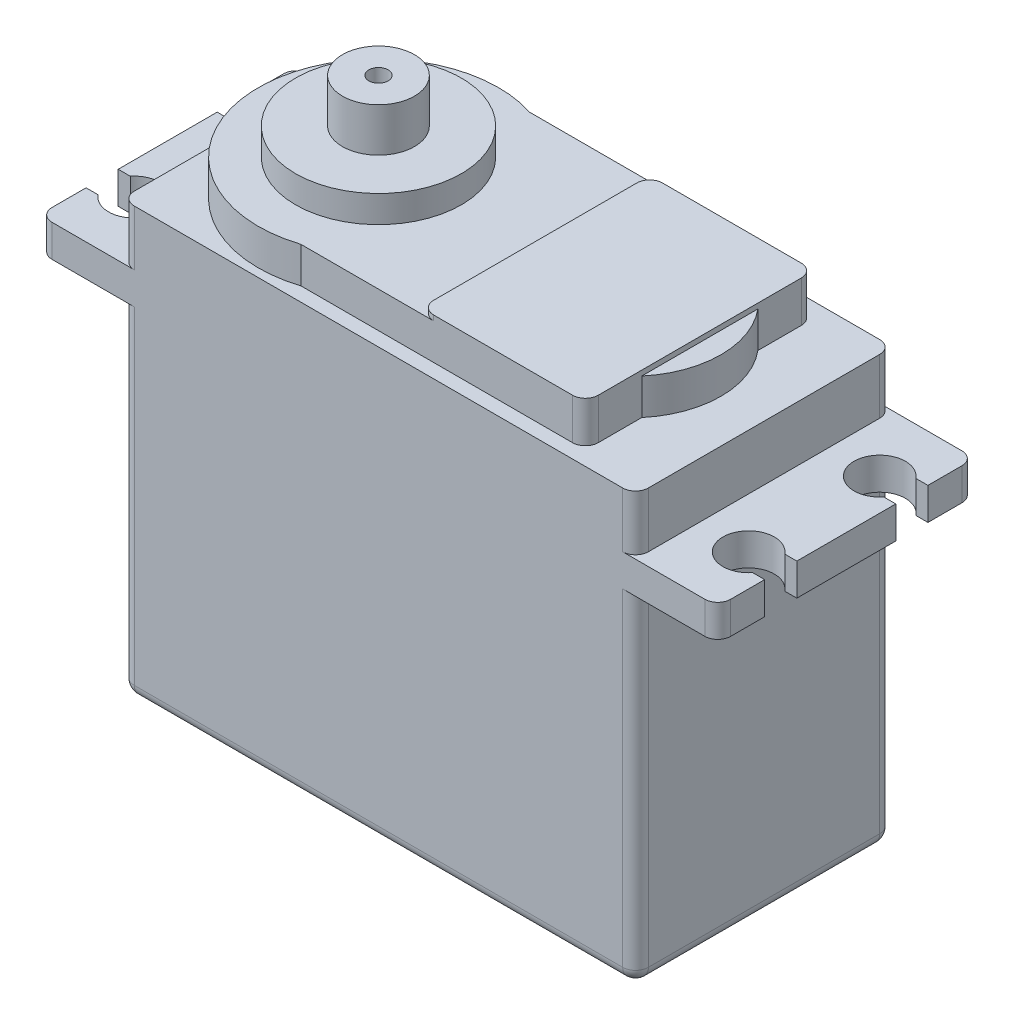
SolidWorks part; units mm, degrees
material "ABS PC"
ref_plane "Спереди" through (0, 0, 0) normal (0, 0, 1) x (1, 0, 0)
ref_plane "Сверху" through (0, 0, 0) normal (0, 1, 0) x (1, 0, 0)
ref_plane "Справа" through (0, 0, 0) normal (1, 0, 0) x (0, 0, -1)
sketch "Эскиз1" plane through (0, 0, 0) normal (0, 1, 0) x (1, 0, 0)
  line L1 (1, 0) -> (39, 0)
  line L2 (0, 1) -> (0, 19)
  line L3 (1, 20) -> (39, 20)
  line L4 (40, 1) -> (40, 19)
  arc A0 (1, 20) -> (0, 19) centre (1, 19) ccw
  arc A1 (40, 19) -> (39, 20) centre (39, 19) ccw
  arc A2 (39, 0) -> (40, 1) centre (39, 1) ccw
  arc A3 (0, 1) -> (1, 0) centre (1, 1) ccw
  point P13 (0, 0)
  dimension "D3" = 1
  dimension "D1" = 40
  dimension "D2" = 20
extrude "Вытянуть1" add sketch "Эскиз1" along normal blind 33.3
sketch "Эскиз2" plane through (0, 0, 0) normal (0, -1, 0) x (1, 0, 0)
  line L1 (-5.4, 0) -> (45.4, 0)
  line L2 (-6.4, -1) -> (-6.4, -19)
  line L3 (-5.4, -20) -> (45.4, -20)
  line L4 (46.4, -1) -> (46.4, -19)
  line L5 (39, -20) -> (1, -20) construction
  line L6 (1, 0) -> (39, 0) construction
  arc A0 (-5.4, 0) -> (-6.4, -1) centre (-5.4, -1) ccw
  arc A1 (46.4, -1) -> (45.4, 0) centre (45.4, -1) ccw
  arc A2 (-5.4, -20) -> (-6.4, -19) centre (-5.4, -19) cw
  arc A3 (46.4, -19) -> (45.4, -20) centre (45.4, -19) cw
  point P4 (20, 0)
  point P5 (20, 0)
  dimension "D2" = 1
  dimension "D1" = 52.8
extrude "Вытянуть2" add sketch "Эскиз2" against normal blind 2.5 from offset 26.5
sketch "Эскиз3" plane through (0, 33.3, 0) normal (0, 1, 0) x (1, 0, 0)
  line L0 (12.8657, 18.9) -> (34, 18.9)
  line L1 (35, 17.9) -> (35, 14.5141)
  line L2 (12.8657, 1.1) -> (34, 1.1)
  line L3 (35, 2.1) -> (35, 5.4859)
  line L5 (0.65, 10) -> (0.65, 20) construction
  line L6 (-5.4, 20) -> (1, 20) construction
  line L7 (0, 19) -> (0, 1) construction
  line L8 (36.65, 10) -> (36.65, 20) construction
  line L9 (40, 10) -> (0, 10) construction
  line L10 (40, 1) -> (40, 19) construction
  line L11 (39, 20) -> (1, 20) construction
  arc A0 (35, 17.9) -> (34, 18.9) centre (34, 17.9) ccw
  arc A1 (35, 14.5141) -> (35, 5.4859) centre (29.65, 10) cw
  arc A2 (12.8657, 18.9) -> (12.8657, 1.1) centre (10, 10) ccw
  arc A3 (34, 1.1) -> (35, 2.1) centre (34, 2.1) ccw
  dimension "D1" = 9.35
  dimension "D3" = 10
  dimension "D4" = 7
  dimension "D7" = 1
  dimension "D2" = 17.8
  dimension "D5" = 36
  dimension "D6" = 5
extrude "Вытянуть3" add sketch "Эскиз3" along normal blind 36.1 from surface at -33.3 contours L0 A2 L2 L3 A1 L1 starting at face at (20, 0, -10)
sketch "Эскиз5" plane through (0, 36.1, 0) normal (0, 1, 0) x (1, 0, 0)
  line L1 (23.2, 18.9) -> (34, 18.9)
  line L2 (22.2, 17.9) -> (22.2, 2.1)
  line L3 (23.2, 1.1) -> (34, 1.1)
  line L4 (35, 17.9) -> (35, 2.1)
  line L5 (12.8657, 1.1) -> (34, 1.1) construction
  line L6 (35, 5.4859) -> (35, 2.1) construction
  line L7 (34, 18.9) -> (12.8657, 18.9) construction
  line L9 (35, 17.9) -> (35, 14.5141) construction
  arc A0 (22.2, 17.9) -> (23.2, 18.9) centre (23.2, 17.9) cw
  arc A1 (23.2, 1.1) -> (22.2, 2.1) centre (23.2, 2.1) cw
  arc A2 (35, 2.1) -> (34, 1.1) centre (34, 2.1) cw
  arc A3 (34, 18.9) -> (35, 17.9) centre (34, 17.9) cw
  point P18 (35, 1.1)
  point P21 (35, 18.9)
  dimension "D2" = 1
  dimension "D1" = 12.8
extrude "Вытянуть4" add sketch "Эскиз5" along normal blind 0.4
sketch "Эскиз6" plane through (0, 36.1, 0) normal (0, 1, 0) x (1, 0, 0)
  circle A0 centre (10, 10) radius 6.45
  arc A1 (12.8657, 18.9) -> (12.8657, 1.1) centre (10, 10) ccw construction
  dimension "D1" = 12.9
extrude "Вытянуть5" add sketch "Эскиз6" along normal blind 2.1
sketch "Эскиз7" plane through (0, 38.2, 0) normal (0, 1, 0) x (1, 0, 0)
  circle A0 centre (10, 10) radius 2.8
  circle A1 centre (10, 10) radius 0.75
  dimension "D1" = 5.6
  dimension "D2" = 1.5
extrude "Вытянуть6" add sketch "Эскиз7" along normal blind 3.4 contours A0 A1
fillet "Скругление1" radius 1 8 edges at (39.7071, 0, -19.7071) (40, 0, -10) (39.7071, 0, -0.2929) (20, 0, 0) (0.2929, 0, -0.2929) (0, 0, -10) (0.2929, 0, -19.7071) (20, 0, -20)
sketch "Эскиз8" plane through (0, 29, 0) normal (0, 1, 0) x (1, 0, 0)
  line L0 (-3.9, 15.1) -> (43.9, 4.9) construction
  line L1 (43.9, 15.1) -> (-3.9, 4.9) construction
  line L2 (20, 20) -> (20, 0) construction
  line L3 (39, 20) -> (1, 20) construction
  line L4 (1, 0) -> (39, 0) construction
  line L5 (46.4, 10) -> (-6.4, 10) construction
  line L6 (46.4, 19) -> (46.4, 1) construction
  line L7 (-6.4, 1) -> (-6.4, 19) construction
  line L8 (45.4612, 16.35) -> (46.4, 16.35)
  line L9 (45.4612, 13.85) -> (46.4, 13.85)
  line L10 (45.4612, 6.15) -> (46.4, 6.15)
  line L11 (45.4612, 3.65) -> (46.4, 3.65)
  line L12 (-5.4612, 16.35) -> (-6.4, 16.35)
  line L13 (-5.4612, 13.85) -> (-6.4, 13.85)
  line L14 (-5.4612, 6.15) -> (-6.4, 6.15)
  line L15 (-5.4612, 3.65) -> (-6.4, 3.65)
  line L16 (45.4612, 16.35) -> (45.4612, 13.85)
  line L17 (46.4, 13.85) -> (46.4, 16.35)
  line L18 (45.4612, 6.15) -> (45.4612, 3.65)
  line L19 (46.4, 6.15) -> (46.4, 3.65)
  line L20 (-5.4612, 16.35) -> (-5.4612, 13.85)
  line L21 (-6.4, 16.35) -> (-6.4, 13.85)
  line L22 (-5.4612, 6.15) -> (-5.4612, 3.65)
  line L23 (-6.4, 6.15) -> (-6.4, 3.65)
  circle A0 centre (-3.9, 15.1) radius 2
  circle A1 centre (-3.9, 4.9) radius 2
  circle A2 centre (43.9, 4.9) radius 2
  circle A3 centre (43.9, 15.1) radius 2
  point P20 (20, 10)
  point P21 (20, 10)
  line M5 (-6.4, 19) -> (-6.4, 1)
  dimension "D1" = 47.8
  dimension "D2" = 10.2
  dimension "D3" = 4
  dimension "D4" = 2.5
extrude "Вырез-Вытянуть1" cut sketch "Эскиз8" against normal up to next contours A1 | A0 | A3 | A2 | A0 L12 L13 M5 | L20 A0 | L22 A1 | A1 L14 L15 M5 | L16 A3 | A3 L9 L17 L8 | L18 A2 | A2 L11 L19 L10
sketch "Эскиз10" plane through (0, 0, 0) normal (-1, 0, 0) x (0, 0, 1)
  line L1 (-12, 0.5) -> (-8, 0.5)
  line L2 (-13, 1.5) -> (-13, 3.5)
  line L3 (-12, 4.5) -> (-8, 4.5)
  line L4 (-7, 1.5) -> (-7, 3.5)
  line L5 (-19, 1) -> (-1, 1) construction
  line L6 (-1, 0) -> (-19, 0) construction
  arc A0 (-13, 3.5) -> (-12, 4.5) centre (-12, 3.5) cw
  arc A1 (-12, 0.5) -> (-13, 1.5) centre (-12, 1.5) cw
  arc A2 (-7, 1.5) -> (-8, 0.5) centre (-8, 1.5) cw
  arc A3 (-8, 4.5) -> (-7, 3.5) centre (-8, 3.5) cw
  point P4 (-10, 0.5)
  point P5 (-10, 1)
  dimension "D3" = 1
  dimension "D1" = 6
  dimension "D2" = 4
  dimension "D4" = 0.5
extrude "Вытянуть7" add sketch "Эскиз10" along normal blind 4.4 and the other way up to next
